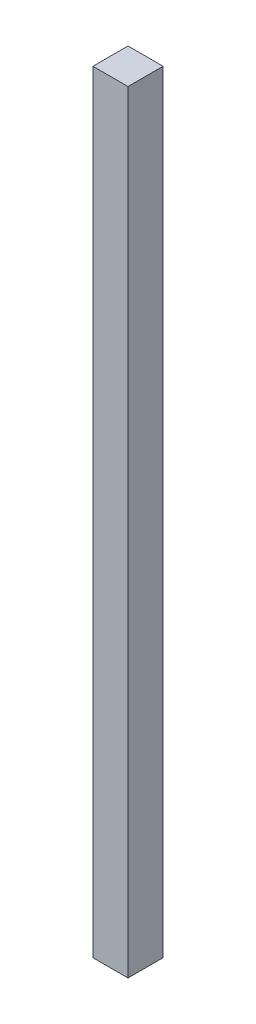
SolidWorks part; units mm, degrees
ref_plane "Plan de face" through (0, 0, 0) normal (0, 0, 1) x (1, 0, 0)
ref_plane "Plan de dessus" through (0, 0, 0) normal (0, 1, 0) x (1, 0, 0)
ref_plane "Plan de droite" through (0, 0, 0) normal (1, 0, 0) x (0, 0, -1)
sketch "Esquisse6" plane through (0, 0, 0) normal (0, 1, 0) x (1, 0, 0)
  line L1 (0, 0) -> (-20, 0)
  line L2 (0, 0) -> (0, 20)
  line L3 (0, 20) -> (-20, 20)
  line L4 (-20, 0) -> (-20, 20)
  dimension "D1" = 20
  dimension "D2" = 20
extrude "Boss.-Extru.1" add sketch "Esquisse6" along normal blind 440
